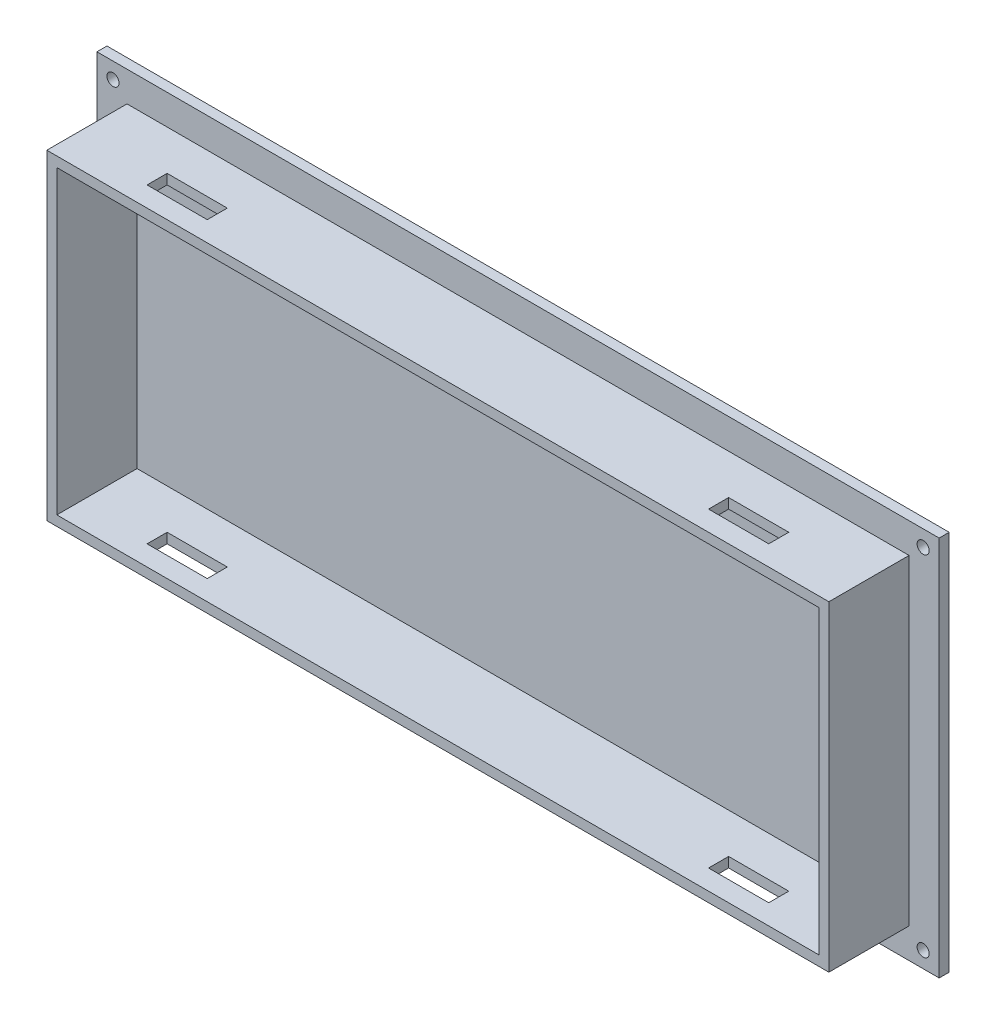
SolidWorks part; units mm, degrees
ref_plane "Front Plane" through (0, 0, 0) normal (0, 0, 1) x (1, 0, 0)
ref_plane "Top Plane" through (0, 0, 0) normal (0, 1, 0) x (1, 0, 0)
ref_plane "Right Plane" through (0, 0, 0) normal (1, 0, 0) x (0, 0, -1)
sketch "Sketch1" plane through (0, 0, 0) normal (0, 0, 1) x (1, 0, 0)
  line L1 (0, 0) -> (210, 0)
  line L2 (0, 0) -> (0, 95)
  line L3 (0, 95) -> (210, 95)
  line L4 (210, 0) -> (210, 95)
  dimension "D1" = 95
  dimension "D2" = 210
extrude "Boss-Extrude1" add sketch "Sketch1" along normal blind 2.5
sketch "Sketch2" plane through (0, 0, 2.5) normal (0, 0, 1) x (1, 0, 0)
  line L0 (0, 47.5) -> (210, 47.5) construction
  line L1 (0, 95) -> (0, 0) construction
  line L2 (210, 0) -> (210, 95) construction
  line L3 (105, 95) -> (105, 0) construction
  line L4 (210, 95) -> (0, 95) construction
  line L5 (0, 0) -> (210, 0) construction
  line L7 (7.5, 87.5) -> (202.5, 87.5)
  line L8 (7.5, 87.5) -> (7.5, 7.5)
  line L9 (7.5, 7.5) -> (202.5, 7.5)
  line L10 (202.5, 87.5) -> (202.5, 7.5)
  dimension "D1" = 7.5
  dimension "D2" = 195
  dimension "D3" = 7.5
  dimension "D4" = 7.5
  dimension "D5" = 80
  dimension "D6" = 7.5
extrude "Boss-Extrude2" add sketch "Sketch2" along normal blind 20
sketch "Sketch3" plane through (0, 0, 22.5) normal (0, 0, 1) x (1, 0, 0)
  line L0 (202.5, 87.5) -> (7.5, 87.5) construction
  line L1 (10, 85) -> (200, 85)
  line L2 (10, 85) -> (10, 10)
  line L3 (10, 10) -> (200, 10)
  line L4 (200, 85) -> (200, 10)
  line L5 (7.5, 87.5) -> (7.5, 7.5) construction
  dimension "D1" = 190
  dimension "D2" = 75
  dimension "D3" = 2.5
  dimension "D4" = 2.5
extrude "Cut-Extrude1" cut sketch "Sketch3" against normal blind 20
sketch "Sketch5" plane through (0, 87.5, 0) normal (0, 1, 0) x (1, 0, 0)
  line L0 (202.5, -22.5) -> (7.5, -22.5) construction
  line L1 (182.5, -17.5) -> (167.5, -17.5)
  line L2 (182.5, -17.5) -> (182.5, -12.5)
  line L3 (182.5, -12.5) -> (167.5, -12.5)
  line L4 (167.5, -17.5) -> (167.5, -12.5)
  line L5 (42.5, -12.5) -> (27.5, -12.5)
  line L6 (42.5, -12.5) -> (42.5, -17.5)
  line L7 (42.5, -17.5) -> (27.5, -17.5)
  line L8 (27.5, -12.5) -> (27.5, -17.5)
  line L9 (202.5, -22.5) -> (202.5, -2.5) construction
  line L10 (7.5, -22.5) -> (7.5, -2.5) construction
  point P8 (175, -17.5)
  dimension "D1" = 15
  dimension "D2" = 5
  dimension "D3" = 15
  dimension "D4" = 5
  dimension "D5" = 5
  dimension "D6" = 20
  dimension "D7" = 20
  dimension "D8" = 5
extrude "Cut-Extrude3" cut sketch "Sketch5" against normal up to surface (80 mm away) up to face at (105, 7.5, 12.5)
sketch "Sketch6" plane through (0, 0, 2.5) normal (0, 0, 1) x (1, 0, 0)
  line L0 (0, 0) -> (210, 0) construction
  line L1 (0, 95) -> (0, 0) construction
  line L2 (210, 95) -> (0, 95) construction
  line L3 (210, 0) -> (210, 95) construction
  circle A0 centre (4, 91) radius 1.5
  circle A1 centre (206, 91) radius 1.5
  circle A2 centre (206, 4) radius 1.5
  circle A3 centre (4, 4) radius 1.5
  dimension "D1" = 3
  dimension "D2" = 3
  dimension "D3" = 3
  dimension "D4" = 3
  dimension "D7" = 4
  dimension "D5" = 4
  dimension "D6" = 4
  dimension "D8" = 4
  dimension "D9" = 4
  dimension "D10" = 4
  dimension "D11" = 4
  dimension "D12" = 4
extrude "Cut-Extrude4" cut sketch "Sketch6" against normal up to surface (2.5 mm away) up to face at (105, 47.5, 0)
